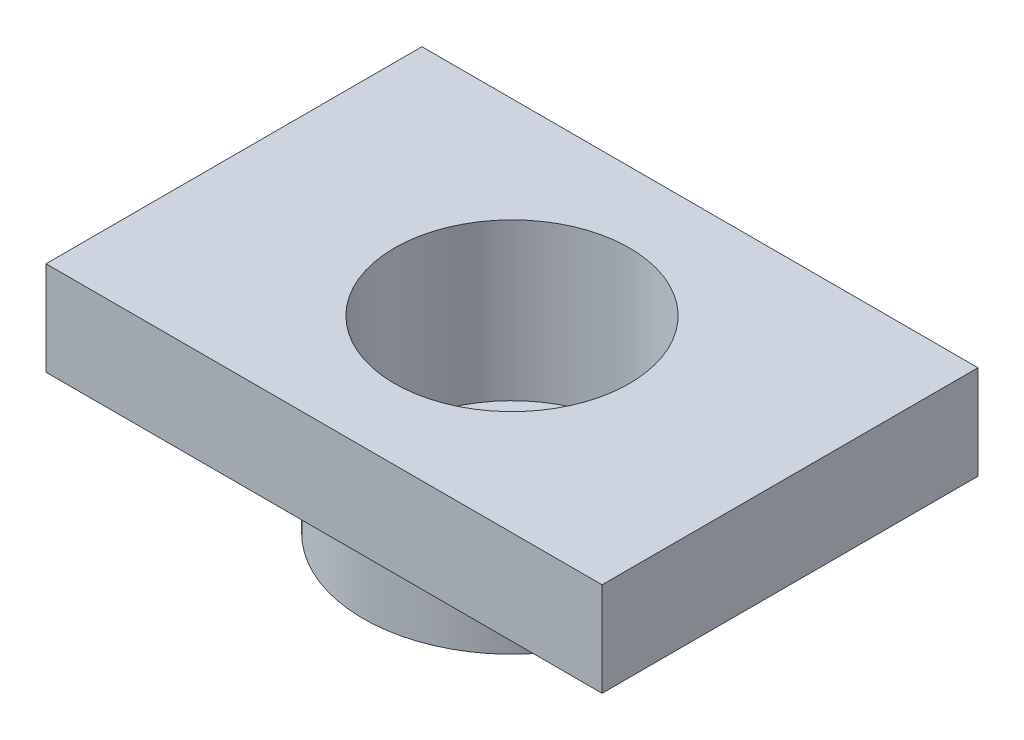
SolidWorks part; units mm, degrees
ref_plane "Plan de face" through (0, 0, 0) normal (0, 0, 1) x (1, 0, 0)
ref_plane "Plan de dessus" through (0, 0, 0) normal (0, 1, 0) x (1, 0, 0)
ref_plane "Plan de droite" through (0, 0, 0) normal (1, 0, 0) x (0, 0, -1)
sketch "Esquisse1" plane through (0, 0, 0) normal (0, 0, 1) x (1, 0, 0)
  line L0 (0, 0) -> (0, -20) construction
  line L1 (19, -12) -> (59, -12)
  line L2 (15, -20) -> (15, 0)
  line L3 (15, -20) -> (9, -20)
  line L5 (59, 0) -> (59, -12)
  line L6 (9, -24) -> (19, -24)
  line L7 (9, -20) -> (9, -24)
  line L9 (19, -24) -> (19, -12)
  line L10 (59, 0) -> (15, 0)
revolve "Révolution1" add sketch "Esquisse1" angle 360 about L0
sketch "Esquisse4" plane through (0, -24, 0) normal (0, -1, 0) x (1, 0, 0)
  line L0 (0, 0) -> (0, 13) construction
  circle A0 centre (0, 13) radius 1.5
  circle A1 centre (13, 0) radius 1.5
  circle A2 centre (0, -13) radius 1.5
  circle A3 centre (-13, 0) radius 1.5
extrude "Extrusion3" cut sketch "Esquisse4" against normal through all
sketch "Esquisse5" plane through (0, -12, 0) normal (0, -1, 0) x (1, 0, 0)
  line L0 (0, 13) -> (13, 0) construction
  line L1 (0, 0) -> (-35.5, 0) construction
  line L2 (-35.5, -24) -> (-35.5, 24)
  line L3 (0, 0) -> (0, -25.8244) construction
  line L4 (35.5, -24) -> (35.5, 24)
  line L5 (35.5, 24) -> (-35.5, 24)
  line L6 (35.5, -24) -> (-35.5, -24)
extrude "Extrusion4" cut sketch "Esquisse5" against normal through all flip side to cut
